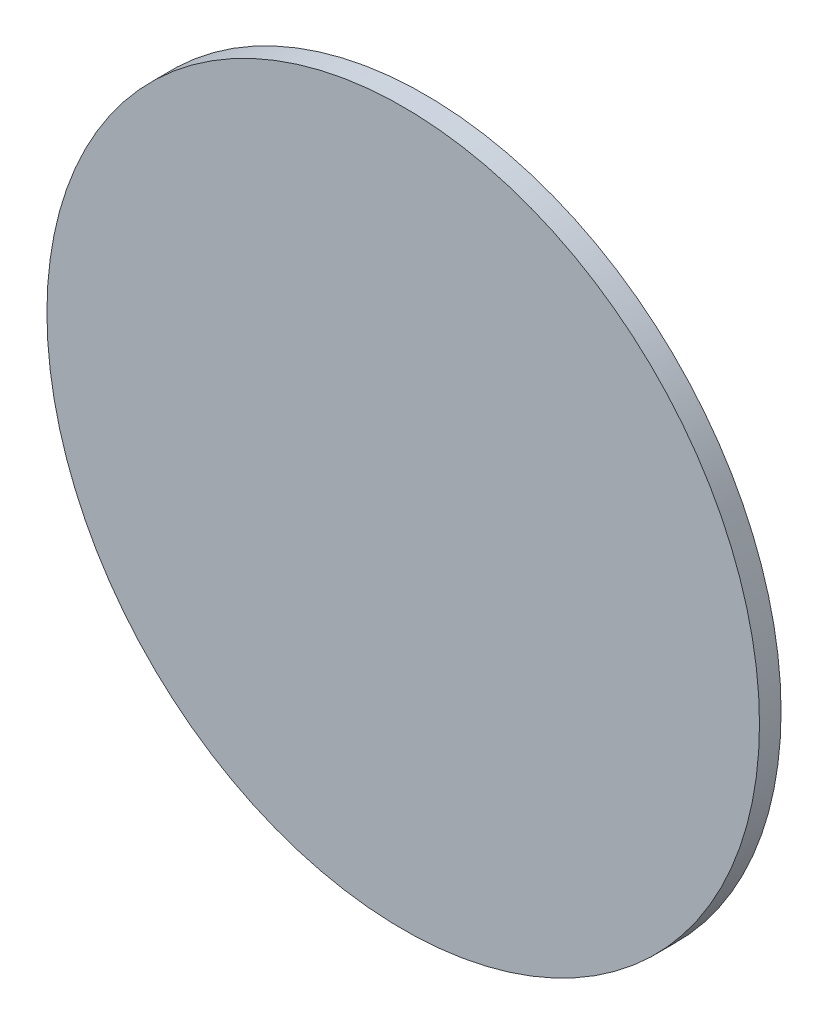
SolidWorks part; units mm, degrees
material "Glass"
ref_plane "Front Plane" through (0, 0, 0) normal (0, 0, 1) x (1, 0, 0)
ref_plane "Top Plane" through (0, 0, 0) normal (0, 1, 0) x (1, 0, 0)
ref_plane "Right Plane" through (0, 0, 0) normal (1, 0, 0) x (0, 0, -1)
sketch "Sketch1" plane through (0, 0, 0) normal (0, 0, 1) x (1, 0, 0)
  circle A0 centre (0, 0) radius 8.382
  dimension "D1" = 16.764
extrude "Boss-Extrude1" add sketch "Sketch1" along normal blind 0.508
